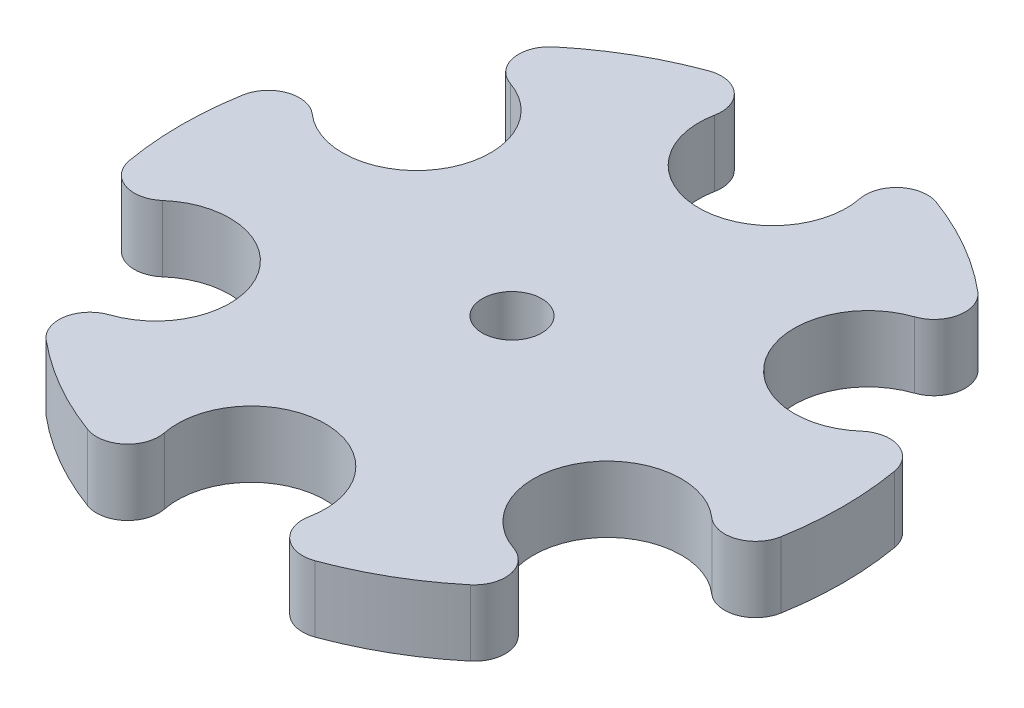
SolidWorks part; units mm, degrees
ref_plane "Alzado" through (0, 0, 0) normal (0, 0, 1) x (1, 0, 0)
ref_plane "Planta" through (0, 0, 0) normal (0, 1, 0) x (1, 0, 0)
ref_plane "Vista lateral" through (0, 0, 0) normal (1, 0, 0) x (0, 0, -1)
sketch "Croquis1" plane through (0, 0, 0) normal (0, 1, 0) x (1, 0, 0)
  line L0 (0, 93.8671) -> (0, -75) construction
  line L1 (-140.5381, 0) -> (179.4923, 0) construction
  arc A1 (-18.6295, 70.7338) -> (18.6295, 70.7338) centre (0, 67) ccw
  arc A2 (-18.6295, 70.7338) -> (-29.224, 79.8183) centre (-26.4735, 72.306) ccw
  arc A3 (18.6295, 70.7338) -> (29.224, 79.8183) centre (26.4735, 72.306) cw
  arc A4 (51.9425, 51.5005) -> (54.5127, 65.2179) centre (49.3821, 59.0797) ccw
  arc A5 (51.9425, 51.5005) -> (70.572, 19.2333) centre (58.0237, 33.5) ccw
  arc A6 (70.572, 19.2333) -> (83.7367, 14.6004) centre (75.8556, 13.2263) cw
  arc A7 (70.572, -19.2333) -> (83.7367, -14.6004) centre (75.8556, -13.2263) ccw
  arc A8 (70.572, -19.2333) -> (51.9425, -51.5005) centre (58.0237, -33.5) ccw
  arc A9 (51.9425, -51.5005) -> (54.5127, -65.2179) centre (49.3821, -59.0797) cw
  arc A10 (18.6295, -70.7338) -> (29.224, -79.8183) centre (26.4735, -72.306) ccw
  arc A11 (18.6295, -70.7338) -> (-18.6295, -70.7338) centre (0, -67) ccw
  arc A12 (-18.6295, -70.7338) -> (-29.224, -79.8183) centre (-26.4735, -72.306) cw
  arc A13 (-51.9425, -51.5005) -> (-54.5127, -65.2179) centre (-49.3821, -59.0797) ccw
  arc A14 (-51.9425, -51.5005) -> (-70.572, -19.2333) centre (-58.0237, -33.5) ccw
  arc A15 (-70.572, -19.2333) -> (-83.7367, -14.6004) centre (-75.8556, -13.2263) cw
  arc A16 (-70.572, 19.2333) -> (-83.7367, 14.6004) centre (-75.8556, 13.2263) ccw
  arc A17 (-70.572, 19.2333) -> (-51.9425, 51.5005) centre (-58.0237, 33.5) ccw
  arc A18 (-51.9425, 51.5005) -> (-54.5127, 65.2179) centre (-49.3821, 59.0797) cw
  arc A26 (-54.5127, -65.2179) -> (-29.224, -79.8183) centre (0, 0) ccw
  arc A27 (-83.7367, 14.6004) -> (-83.7367, -14.6004) centre (0, 0) ccw
  arc A28 (-54.5127, -65.2179) -> (-29.224, -79.8183) centre (0, 0) ccw
  arc A29 (29.224, -79.8183) -> (54.5127, -65.2179) centre (0, 0) ccw
  arc A30 (54.5127, 65.2179) -> (29.224, 79.8183) centre (0, 0) ccw
  arc A31 (83.7367, -14.6004) -> (83.7367, 14.6004) centre (0, 0) ccw
  arc A32 (54.5127, 65.2179) -> (29.224, 79.8183) centre (0, 0) ccw
  arc A33 (-29.224, 79.8183) -> (-54.5127, 65.2179) centre (0, 0) ccw
  arc A34 (29.224, -79.8183) -> (54.5127, -65.2179) centre (0, 0) ccw
  arc A35 (83.7367, -14.6004) -> (83.7367, 14.6004) centre (0, 0) ccw
  circle A38 centre (0, 0) radius 7.65
  point P14 (58.0237, -33.5)
  point P15 (58.0237, 33.5)
  point P19 (0, -67)
  point P21 (-58.0237, -33.5)
  point P25 (-58.0237, 33.5)
  point P27 (-49.3821, 59.0797)
  point P31 (-26.4735, 72.306)
  point P33 (49.3821, 59.0797)
  point P37 (26.4735, 72.306)
  point P39 (75.8556, 13.2263)
  point P46 (75.8556, -13.2263)
  point P48 (49.3821, -59.0797)
  point P52 (26.4735, -72.306)
  point P54 (-26.4735, -72.306)
  point P55 (-49.3821, -59.0797)
  point P56 (-75.8556, 13.2263)
  point P57 (-75.8556, -13.2263)
  point P58 (0, 0)
  dimension "D1" = 85
  dimension "D2" = 38
  dimension "D3" = 6
  dimension "D4" = 8
  dimension "D5" = 15.3
  dimension "D6" = 67
extrude "Saliente-Extruir1" add sketch "Croquis1" along normal mid plane 17 contours A2 A33 A18 A17 A16 A27 A15 A14 A13 A26 A12 A11 A10 A29 A9 A8 A7 A31 A6 A5 A4 A30 A3 A1 A38
sketch "Croquis2" plane through (0, 0, 0) normal (0, 1, 0) x (1, 0, 0)
  circle A2 centre (0, 0) radius 5
  circle A3 centre (0, 0) radius 7.65 construction
  circle A4 centre (0, 0) radius 7.65
  dimension "D1" = 10
extrude "Saliente-Extruir2" add sketch "Croquis2" along normal blind 21.5 separate body
mirror "Simetría3" about plane through (0, 0, 0) normal (0, 1, 0) of bodies 102
sketch "Croquis3" plane through (0, 0, 0) normal (0, 0, 1) x (1, 0, 0)
  line L0 (7.65, 21.5) -> (-7.65, 21.5) construction
  line L1 (0, 10.9585) -> (3.5, 12.9793)
  line L2 (3.5, 12.9793) -> (3.5, 17.0207)
  line L3 (3.5, 17.0207) -> (0, 19.0415)
  line L4 (0, 19.0415) -> (-3.5, 17.0207)
  line L5 (-3.5, 17.0207) -> (-3.5, 12.9793)
  line L6 (-3.5, 12.9793) -> (0, 10.9585)
  line L8 (0, 15) -> (0, 21.5) construction
  line L10 (19, 8.5) -> (-19, 8.5) construction
  circle A0 centre (0, 15) radius 3.5 construction
  circle A1 centre (0, 15) radius 6.5
  dimension "D1" = 7
  dimension "D2" = 3
extrude "Saliente-Extruir3" add sketch "Croquis3" against normal up to next from offset 12
sketch "Croquis4" plane through (0, 0, 12) normal (0, 0, 1) x (1, 0, 0)
  circle A0 centre (0, 15) radius 2.25
  dimension "D1" = 4.5
extrude "Cortar-Extruir1" cut sketch "Croquis4" against normal up to next
delete or keep bodies "Sólido-Eliminar/Conservar 1" type delete bodies bodies 105
delete or keep bodies "Sólido-Eliminar/Conservar 2" [suppressed] type delete bodies bodies 101
mirror "Simetría4" [suppressed] about plane through (0, 0, 0) normal (0, 0, 1)
